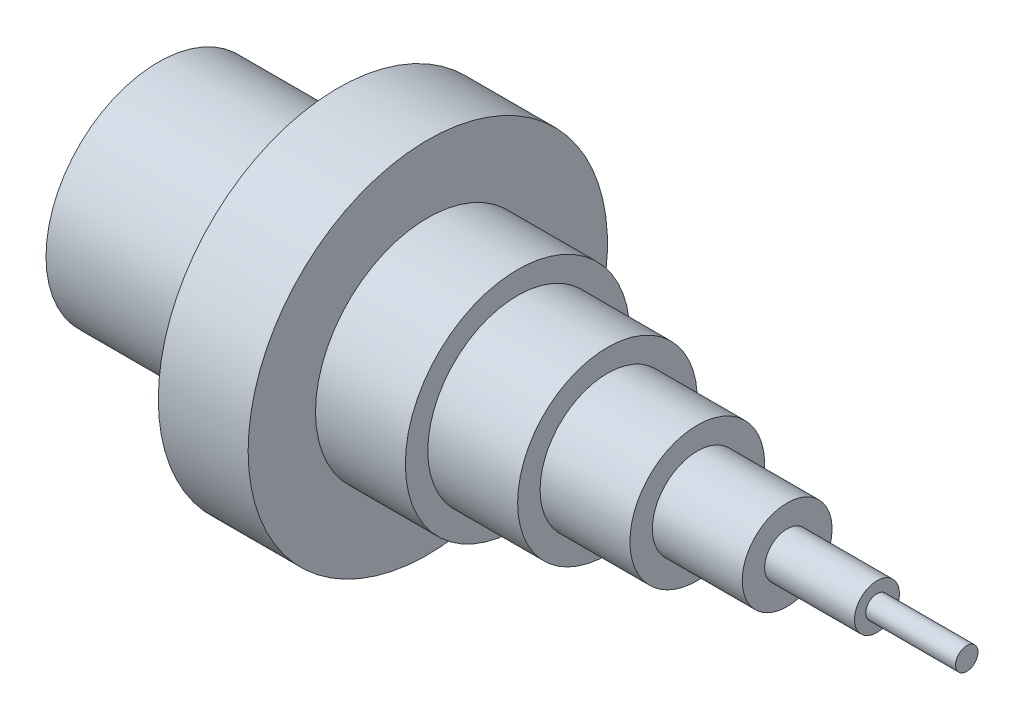
SolidWorks part; units mm, degrees
ref_plane "Front Plane" through (0, 0, 0) normal (0, 0, 1) x (1, 0, 0)
ref_plane "Top Plane" through (0, 0, 0) normal (0, 1, 0) x (1, 0, 0)
ref_plane "Right Plane" through (0, 0, 0) normal (1, 0, 0) x (0, 0, -1)
sketch "Sketch1" plane through (0, 0, 0) normal (0, 1, 0) x (1, 0, 0)
  line L0 (0, 0) -> (0, 25)
  line L1 (0, 25) -> (40, 25)
  line L2 (40, 25) -> (40, 40)
  line L3 (40, 40) -> (60, 40)
  line L4 (60, 40) -> (60, 25)
  line L5 (60, 25) -> (80, 25)
  line L6 (80, 25) -> (80, 20)
  line L7 (80, 20) -> (100, 20)
  line L8 (100, 20) -> (100, 15)
  line L9 (100, 15) -> (120, 15)
  line L10 (120, 15) -> (120, 10)
  line L11 (120, 10) -> (140, 10)
  line L12 (140, 10) -> (140, 5)
  line L13 (140, 5) -> (160, 5)
  line L14 (160, 5) -> (160, 2.5)
  line L15 (160, 2.5) -> (180, 2.5)
  line L16 (180, 2.5) -> (180, 0)
  line L17 (180, 0) -> (0, 0)
  line L18 (-28.8889, 0) -> (136.1111, 0) construction
  dimension "D2" = 50
  dimension "D3" = 40
  dimension "D4" = 25
  dimension "D5" = 20
  dimension "D6" = 15
  dimension "D7" = 10
  dimension "D8" = 5
  dimension "D9" = 40
  dimension "D10" = 20
  dimension "D11" = 20
  dimension "D12" = 20
  dimension "D13" = 20
  dimension "D14" = 20
  dimension "D15" = 20
  dimension "D16" = 180
  dimension "D17" = 2.5
revolve "Revolve1" add sketch "Sketch1" angle 360 about L18
sketch "Sketch2" plane through (0, 0, 0) normal (-1, 0, 0) x (0, 0, 1)
  circle A0 centre (0, 0) radius 20
  dimension "D1" = 40
extrude "Cut-Extrude1" cut sketch "Sketch2" against normal blind 40
